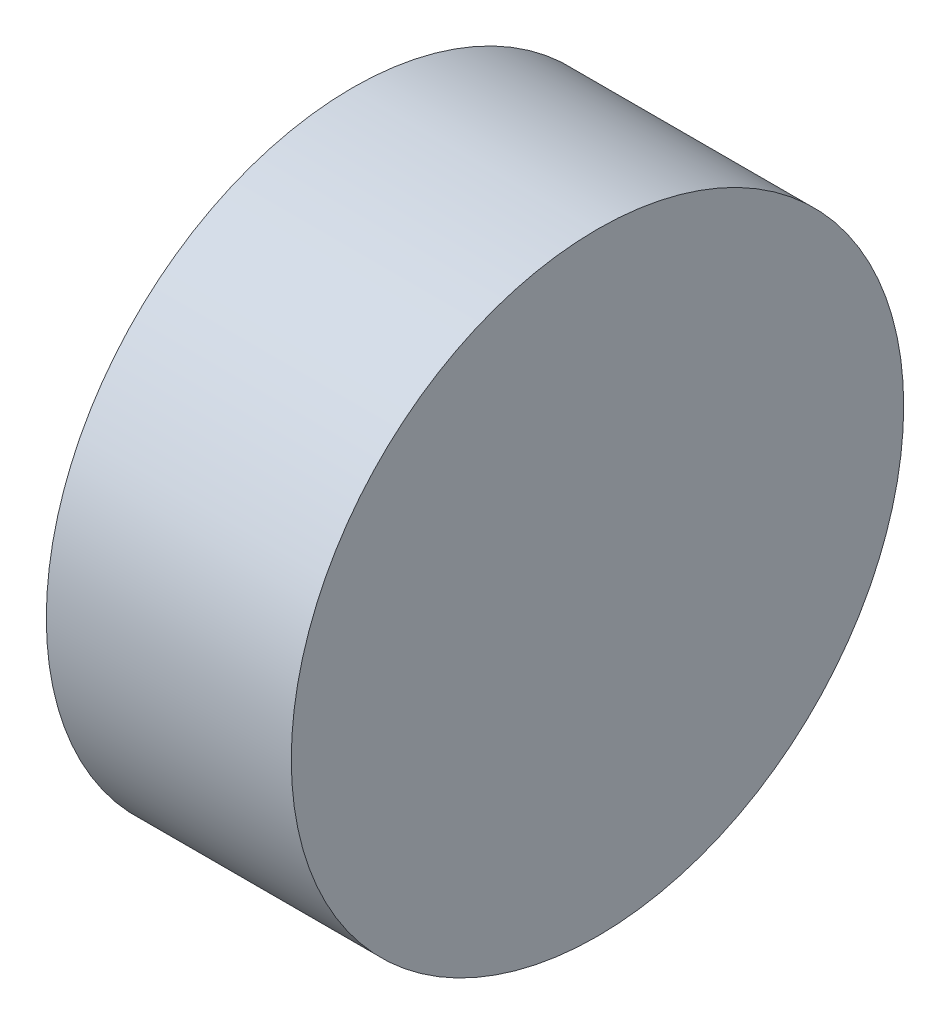
SolidWorks part; units mm, degrees
ref_plane "前视基准面" through (0, 0, 0) normal (0, 0, 1) x (1, 0, 0)
ref_plane "上视基准面" through (0, 0, 0) normal (0, 1, 0) x (1, 0, 0)
ref_plane "右视基准面" through (0, 0, 0) normal (1, 0, 0) x (0, 0, -1)
sketch "草图1" plane through (0, 0, 0) normal (0, 0, 1) x (1, 0, 0)
  line L0 (54.0314, 15.4586) -> (52.0314, 15.4586)
  line L10 (50.8002, 15.4586) -> (55.2877, 15.4586) construction
  line L11 (52.0314, 15.4586) -> (52.0314, 17.9586)
  line L12 (52.0314, 17.9586) -> (54.0314, 17.9586)
  line L13 (54.0314, 17.9586) -> (54.0314, 15.4586)
  dimension "D1" = 2
  dimension "D2" = 2.5
revolve "旋转1" add sketch "草图1" angle 360 about L10
